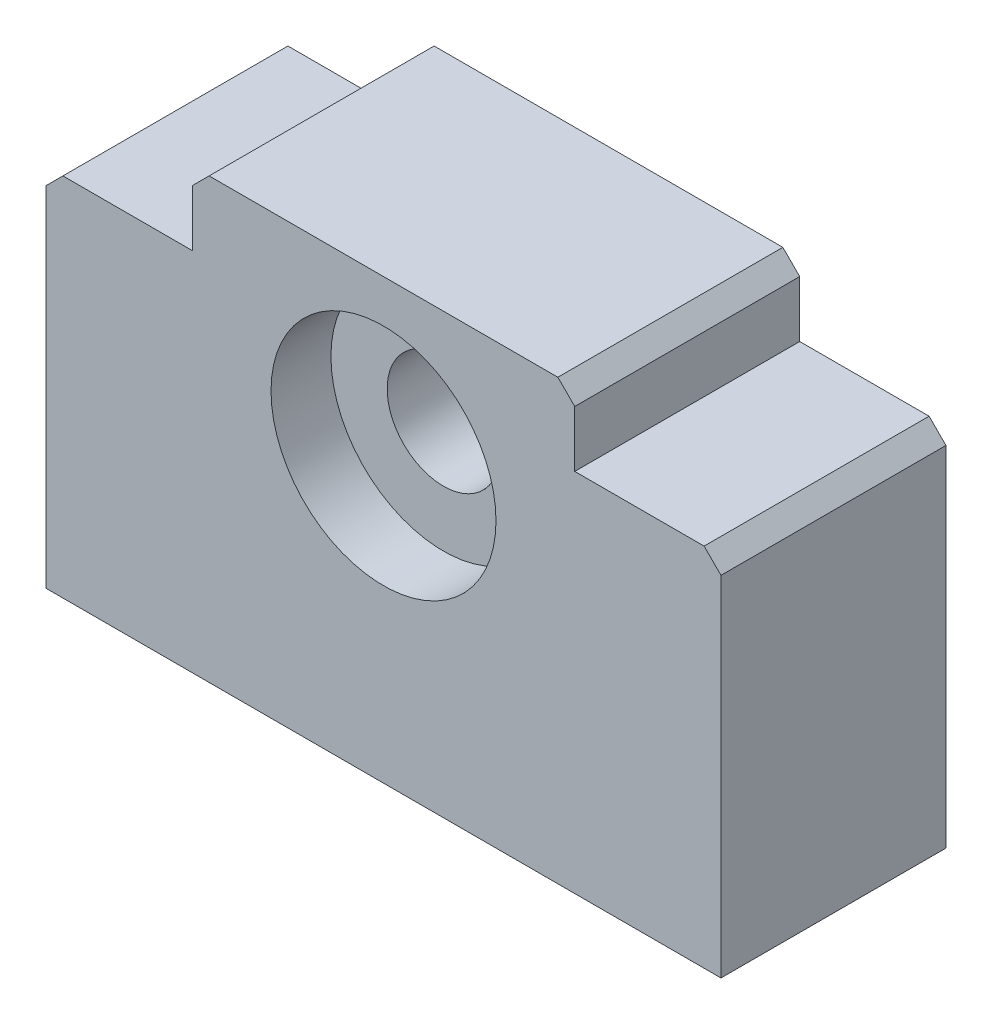
SolidWorks part; units mm, degrees
material "AISI 1045 Acero estirado en frío"
ref_plane "Alzado" through (0, 0, 0) normal (0, 0, 1) x (1, 0, 0)
ref_plane "Planta" through (0, 0, 0) normal (0, 1, 0) x (1, 0, 0)
ref_plane "Vista lateral" through (0, 0, 0) normal (1, 0, 0) x (0, 0, -1)
sketch "Croquis1" plane through (0, 0, 0) normal (0, 0, 1) x (1, 0, 0)
  line L0 (30, -16.25) -> (30, 8.75) construction
  line L1 (-30, 16.25) -> (-17, 16.25)
  line L2 (-30, 16.25) -> (-30, -16.25)
  line L3 (-30, -16.25) -> (30, -16.25)
  line L4 (30, 16.25) -> (30, -16.25)
  line L5 (-30, 16.25) -> (30, -16.25) construction
  line L6 (-30, -16.25) -> (30, 16.25) construction
  line L7 (30, 8.75) -> (-30, 8.75) construction
  line L8 (-17, 16.25) -> (-17, 22.75)
  line L9 (-17, 22.75) -> (17, 22.75)
  line L10 (17, 22.75) -> (17, 16.25)
  line L11 (17, 16.25) -> (30, 16.25)
  line L12 (0, 22.75) -> (0, 8.75) construction
  point P0 (0, 0)
  dimension "D1" = 60
  dimension "D2" = 32.5
  dimension "D3" = 6.5
  dimension "D4" = 25
extrude "Saliente-Extruir1" add sketch "Croquis1" along normal blind 20
sketch "Croquis2" plane through (0, 0, 0) normal (0, 0, 1) x (1, 0, 0)
  line L0 (-30, -16.25) -> (-30, 8.95) construction
  line L1 (-30, 16.25) -> (-30, -16.25) construction
  line L2 (-30, 8.95) -> (0, 8.95) construction
  line L3 (0, 8.95) -> (0, 22.75) construction
  line L4 (17, 22.75) -> (-17, 22.75) construction
  circle A0 centre (0, 8.95) radius 5
  dimension "D2" = 10
  dimension "D1" = 25.2
extrude "Cortar-Extruir1" cut sketch "Croquis2" along normal through all
chamfer "Chaflán1" distance 1.5 angle 45 4 edges at (30, 16.25, 10) (17, 22.75, 10) (-17, 22.75, 10) (-30, 16.25, 10)
sketch "Croquis3" plane through (0, 0, 0) normal (0, 0, 1) x (1, 0, 0)
  line L0 (0, 0) -> (0, 17.7039) construction
  line L1 (-7.592, 8.852) -> (8.3706, 8.852) construction
  circle A0 centre (0, 8.852) radius 10
  dimension "D1" = 20
extrude "Cortar-Extruir2" cut sketch "Croquis3" along normal blind 5.325
ref_plane "Plano1" through (0, 0, 20) normal (0, 0, 1) x (1, 0, 0)
sketch "Croquis5" plane through (0, 0, 20) normal (0, 0, 1) x (1, 0, 0)
  circle A0 centre (0, 8.95) radius 10
  dimension "D1" = 20
extrude "Cortar-Extruir3" cut sketch "Croquis5" against normal blind 5.325
